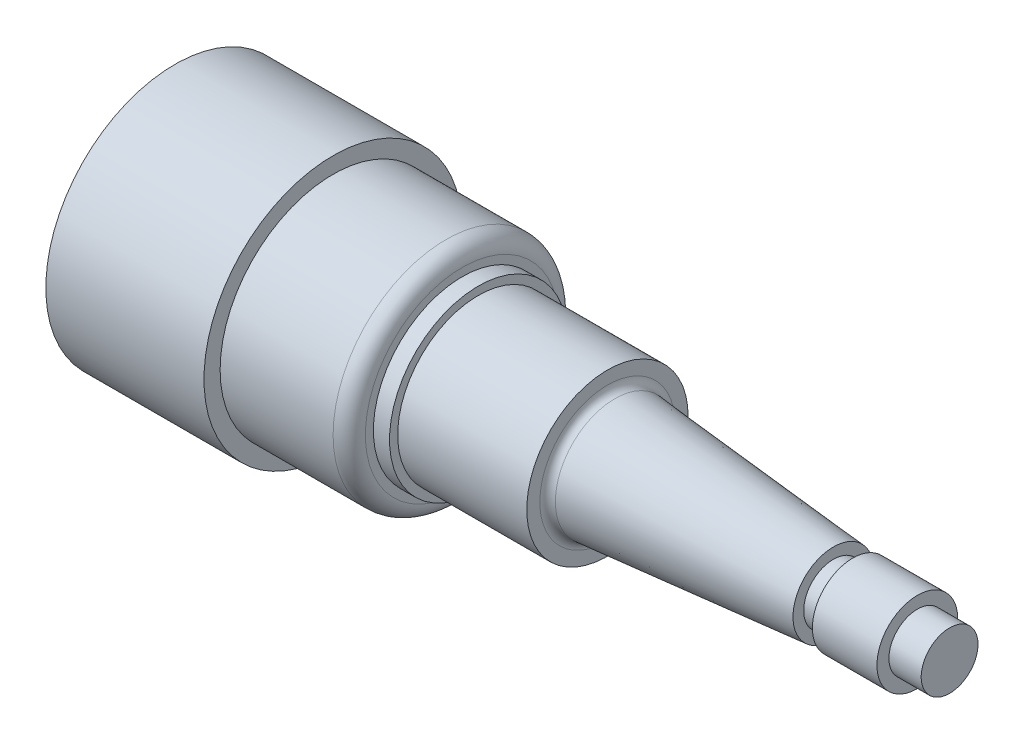
SolidWorks part; units mm, degrees
ref_plane "Front Plane" through (0, 0, 0) normal (0, 0, 1) x (1, 0, 0)
ref_plane "Top Plane" through (0, 0, 0) normal (0, 1, 0) x (1, 0, 0)
ref_plane "Right Plane" through (0, 0, 0) normal (1, 0, 0) x (0, 0, -1)
ref_axis "Axis1" through (88.99, 0, 0) along (-1, 0, 0)
sketch "Sketch2" plane through (0, 0, 0) normal (0, 0, 1) x (1, 0, 0)
  line L0 (-152.4, 0) -> (0, 0)
  line L4 (-121.285, -22.225) -> (-121.285, -25.4)
  line L5 (-95.885, -17.4752) -> (-92.71, -17.4752)
  line L6 (-121.285, -22.225) -> (-99.06, -22.225)
  line L7 (-95.885, -17.4752) -> (-95.885, -19.05)
  line L8 (0, 0) -> (0, -5.588)
  line L9 (-6.35, -5.588) -> (-6.35, -7.9502)
  line L10 (-88.5729, 0) -> (85.2375, 0) construction
  line L14 (-88.5729, -17.4752) -> (85.2375, -17.4752) construction
  line L15 (-88.5729, -22.225) -> (85.2375, -22.225) construction
  line L16 (-92.71, 0) -> (-92.71, -25.4) construction
  line L17 (-19.05, -5.842) -> (-19.05, -7.9502)
  line L18 (-22.86, -5.842) -> (-22.86, -7.9502)
  line L19 (-67.31, -13.3035) -> (-67.31, -15.875)
  line L20 (-92.71, -15.875) -> (-92.71, -17.4752)
  line L23 (-6.35, -5.588) -> (0, -5.588)
  line L25 (0, 0) -> (0, -25.4) construction
  line L26 (-6.35, 0) -> (-6.35, -25.4) construction
  line L27 (-19.05, -7.9502) -> (-6.35, -7.9502)
  line L28 (-19.05, 0) -> (-19.05, -25.4) construction
  line L29 (-22.86, 0) -> (-22.86, -25.4) construction
  line L30 (-22.86, -7.9502) -> (-65.8492, -11.7094)
  line L33 (-67.31, 0) -> (-67.31, -25.4) construction
  line L34 (-22.86, -5.842) -> (-19.05, -5.842)
  line L35 (-92.71, -15.875) -> (-67.31, -15.875)
  line L36 (-121.285, -25.4) -> (-152.4, -25.4)
  line L37 (-152.4, -25.4) -> (-152.4, 0)
  arc A0 (-67.31, -13.3035) -> (-65.8492, -11.7094) centre (-65.7098, -13.3035) cw
  arc A1 (-95.885, -19.05) -> (-99.06, -22.225) centre (-99.06, -19.05) cw
  point P5 (-88.5729, -6.35)
  point P6 (85.2375, -6.35)
  point P7 (-88.5729, -3.81)
  point P8 (85.2375, -3.81)
  point P9 (-88.5729, -12.7)
  point P10 (85.2375, -12.7)
  point P15 (-88.5729, -25.4)
  point P16 (85.2375, -25.4)
  point P36 (-121.285, 0)
  point P45 (-121.285, -5.08)
  point P46 (0, -5.08)
  dimension "D15" = 1.6002
  dimension "D16" = 3.175
  dimension "D2" = 7.9502
  dimension "D3" = 5.588
  dimension "D6" = 15.875
  dimension "D12" = 11.7094
  dimension "D13" = 7.9502
  dimension "D14" = 5.842
  dimension "D17" = 4.998
  dimension "D18" = 121.285
  dimension "D19" = 152.4
  dimension "D4" = 17.4752
  dimension "D5" = 22.225
  dimension "D7" = 6.35
  dimension "D8" = 19.05
  dimension "D9" = 22.86
  dimension "D10" = 67.31
  dimension "D11" = 92.71
revolve "Revolve1" add sketch "Sketch2" angle 360 about axis through (88.99, 0, 0) along (-1, 0, 0)
